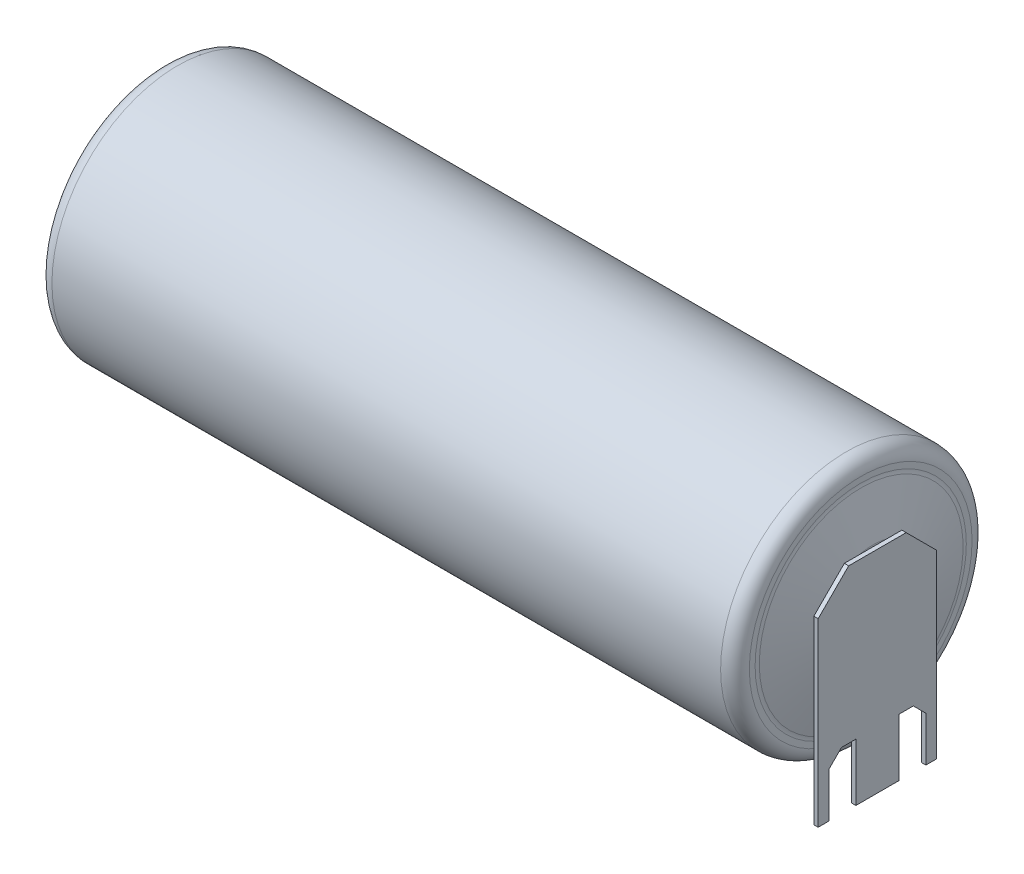
SolidWorks part; units mm, degrees
ref_plane "Front Plane" through (0, 0, 0) normal (0, 0, 1) x (1, 0, 0)
ref_plane "Top Plane" through (0, 0, 0) normal (0, 1, 0) x (1, 0, 0)
ref_plane "Right Plane" through (0, 0, 0) normal (1, 0, 0) x (0, 0, -1)
sketch "Sketch1" plane through (0, 0, 0) normal (0, 0, 1) x (1, 0, 0)
  line L0 (-25.5, 0) -> (24.7, 0)
  line L1 (24.6376, 7.75) -> (24.6376, 7.35)
  line L2 (-22.9, 8.75) -> (23.6376, 8.75)
  line L3 (25.5, 0.5) -> (-25.5, 0.5) construction
  line L4 (0, 0) -> (0, 0.5) construction
  line L5 (-23.9, 7.75) -> (-23.9, 6.85)
  line L6 (-23.8, 6.75) -> (-23.5, 6.75)
  line L7 (24.6717, 7.0912) -> (25.4864, 4.0509)
  line L8 (25.5, 3.9473) -> (25.5, 0.9)
  line L9 (25.4, 0.8) -> (24.8, 0.8)
  line L10 (24.7, 0.7) -> (24.7, 0)
  line L11 (-25.5, 0) -> (-25.5, 2.1)
  line L12 (-23.4, 6.65) -> (-23.4, 4.35)
  line L13 (-25.1, 2.5) -> (-24.1, 2.5)
  line L14 (-23.7, 2.9) -> (-23.7, 4.15)
  line L15 (-23.6, 4.25) -> (-23.5, 4.25)
  arc A0 (-23.9, 7.75) -> (-22.9, 8.75) centre (-22.9, 7.75) cw
  arc A1 (25.4864, 4.0509) -> (25.5, 3.9473) centre (25.1, 3.9473) cw
  arc A2 (-23.7, 2.9) -> (-24.1, 2.5) centre (-24.1, 2.9) cw
  arc A3 (-25.5, 2.1) -> (-25.1, 2.5) centre (-25.1, 2.1) cw
  arc A4 (23.6376, 8.75) -> (24.6376, 7.75) centre (23.6376, 7.75) cw
  arc A5 (24.6717, 7.0912) -> (24.6376, 7.35) centre (25.6376, 7.35) cw
  arc A6 (24.7, 0.7) -> (24.8, 0.8) centre (24.8, 0.7) cw
  arc A7 (25.5, 0.9) -> (25.4, 0.8) centre (25.4, 0.9) cw
  arc A8 (-23.9, 6.85) -> (-23.8, 6.75) centre (-23.8, 6.85) ccw
  arc A9 (-23.5, 6.75) -> (-23.4, 6.65) centre (-23.5, 6.65) cw
  arc A10 (-23.5, 4.25) -> (-23.4, 4.35) centre (-23.5, 4.35) ccw
  arc A11 (-23.6, 4.25) -> (-23.7, 4.15) centre (-23.6, 4.15) ccw
  point P5 (24.6376, 7.2183)
  point P20 (25.5, 4)
  point P26 (-23.9, 8.75)
  point P30 (24.6376, 7.2183)
  point P37 (-23.9, 6.75)
  dimension "D8" = 8.75
  dimension "D4" = 1
  dimension "D5" = 1
  dimension "D16" = 0.4
  dimension "D17" = 0.1
  dimension "D1" = 0.8
  dimension "D2" = 0.8
  dimension "D3" = 15
  dimension "D6" = 4
  dimension "D7" = 2
  dimension "D9" = 0.5
  dimension "D10" = 2.5
  dimension "D11" = 4.25
  dimension "D12" = 1.6
  dimension "D13" = 0.3
  dimension "D14" = 51
  dimension "D15" = 0.4
  dimension "D18" = 0.5
revolve "Revolve1" add sketch "Sketch1" angle 360 about L0
sketch "Sketch2" plane through (25.5, 0, 0) normal (1, 0, 0) x (0, 0, -1)
  line L0 (0, 0) -> (0, 3.9473) construction
  line L1 (-2, 3.9473) -> (2, 3.9473)
  line L2 (-1.5, -6.75) -> (-1.5, -10.75)
  line L3 (-1.5, -10.75) -> (1.5, -10.75)
  line L4 (1.5, -6.75) -> (1.5, -10.75)
  line L5 (0, -8.75) -> (0, 0) construction
  line L6 (1.5, -6.75) -> (2.5, -6.75)
  line L7 (2.5, -6.75) -> (3.375, -7.625)
  line L8 (3.375, -7.625) -> (3.375, -10.75)
  line L9 (3.375, -10.75) -> (4.125, -10.75)
  line L10 (4.125, -10.75) -> (4.125, 1.8223)
  line L11 (4.125, 1.8223) -> (2, 3.9473)
  line L12 (-4.125, 1.8223) -> (-2, 3.9473)
  line L13 (-4.125, 1.8223) -> (-4.125, -10.75)
  line L14 (-4.125, -10.75) -> (-3.375, -10.75)
  line L15 (-3.375, -10.75) -> (-3.375, -7.625)
  line L16 (-3.375, -7.625) -> (-2.5, -6.75)
  line L17 (-2.5, -6.75) -> (-1.5, -6.75)
  line L18 (3.75, -10.75) -> (3.75, -12.3309) construction
  line L19 (-3.75, -10.75) -> (-3.75, -11.7379) construction
  line L20 (0, -8.75) -> (0, -10.75) construction
  circle A0 centre (0, 0) radius 8.75 construction
  circle A1 centre (0, 0) radius 3.9473 construction
  point P7 (0, -8.75)
  dimension "D1" = 2
  dimension "D2" = 3
  dimension "D3" = 7.5
  dimension "D4" = 0.75
  dimension "D5" = 45
  dimension "D6" = 1
  dimension "D7" = 4
  dimension "D8" = 45
  dimension "D9" = 4
extrude "Boss-Extrude1" add sketch "Sketch2" along normal blind 0.3
sketch "Sketch3" plane through (-25.5, 0, 0) normal (-1, 0, 0) x (0, 0, 1)
  line L1 (-1.5, 2.25) -> (1.5, 2.25)
  line L2 (-1.5, 2.25) -> (-1.5, -10.75)
  line L3 (-1.5, -10.75) -> (1.5, -10.75)
  line L4 (1.5, 2.25) -> (1.5, -10.75)
  dimension "D1" = 13
extrude "Boss-Extrude2" add sketch "Sketch3" along normal blind 0.3
